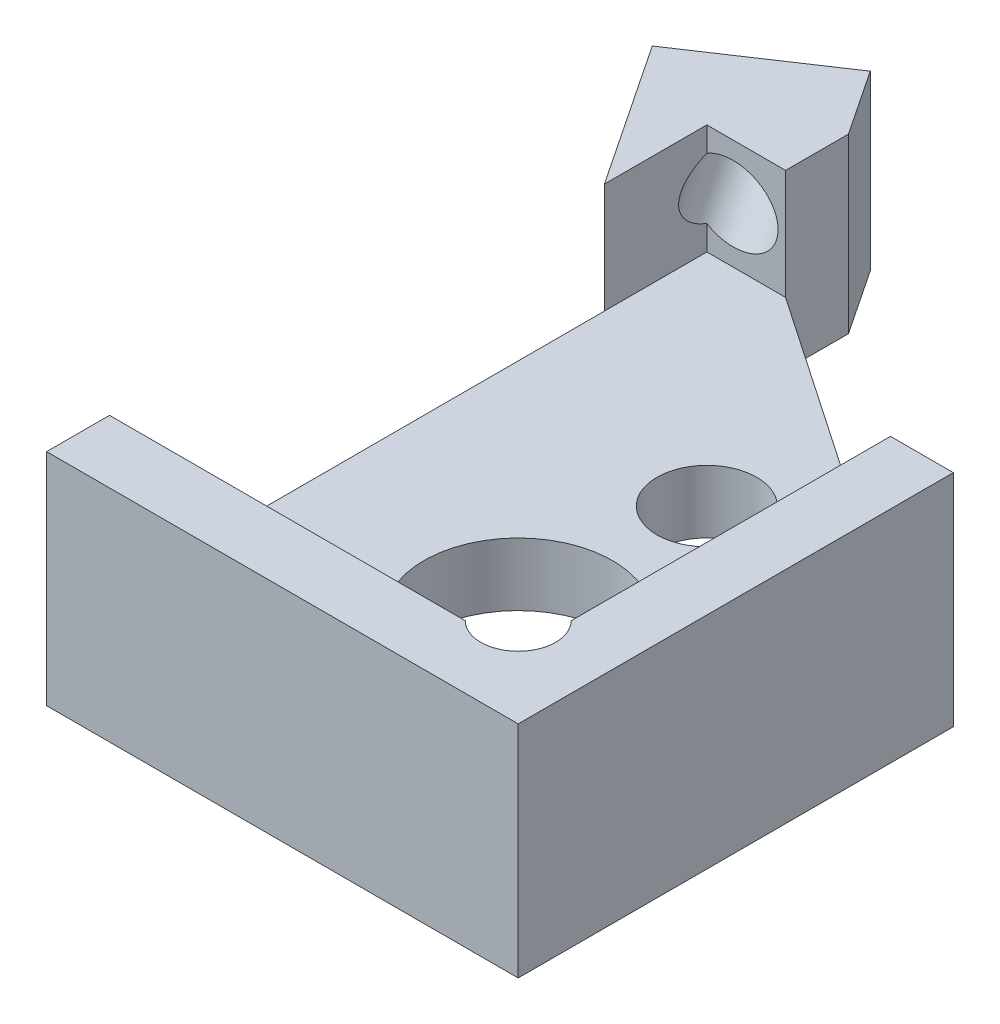
SolidWorks part; units mm, degrees
ref_plane "Front Plane" through (0, 0, 0) normal (0, 0, 1) x (1, 0, 0)
ref_plane "Top Plane" through (0, 0, 0) normal (0, 1, 0) x (1, 0, 0)
ref_plane "Right Plane" through (0, 0, 0) normal (1, 0, 0) x (0, 0, -1)
sketch "Sketch1" plane through (0, 0, 0) normal (0, 1, 0) x (1, 0, 0)
  line L7 (4.25, 5.75) -> (-4.25, 5.75)
  line L8 (4.25, 5.75) -> (4.25, -5.75)
  line L9 (4.25, -5.75) -> (-4.25, -5.75)
  line L10 (-4.25, 5.75) -> (-4.25, -5.75)
  line L11 (4.25, 5.75) -> (-4.25, -5.75) construction
  line L12 (4.25, -5.75) -> (-4.25, 5.75) construction
  point P0 (0, 0)
  point P6 (0, 0)
  dimension "D1" = 8.5
  dimension "D2" = 11.5
extrude "Boss-Extrude1" add sketch "Sketch1" along normal blind 3.5
sketch "Sketch2" plane through (0, 3.5, 0) normal (0, 1, 0) x (1, 0, 0)
  line L0 (-4.25, 5.75) -> (-4.25, -5.75) construction
  line L1 (3.25, 4.75) -> (-3.25, 4.75)
  line L2 (3.25, 4.75) -> (3.25, -4.75)
  line L3 (3.25, -4.75) -> (-3.25, -4.75)
  line L4 (-3.25, 4.75) -> (-3.25, -4.75)
  line L5 (3.25, 4.75) -> (-3.25, -4.75) construction
  line L6 (3.25, -4.75) -> (-3.25, 4.75) construction
  line L7 (4.25, 5.75) -> (-4.25, 5.75) construction
  point P0 (0, 0)
  dimension "D1" = 1
  dimension "D2" = 1
extrude "Cut-Extrude1" cut sketch "Sketch2" against normal offset from surface (2.5 mm away) 1 up to face at (0, 0, 0)
sketch "Sketch3" plane through (0, 1, 0) normal (0, 1, 0) x (1, 0, 0)
  line L0 (-3.25, -4.75) -> (3.25, -4.75) construction
  line L1 (3.25, -4.75) -> (3.25, 4.75) construction
  circle A0 centre (0.25, -1.75) radius 1.5
  dimension "D1" = 3
  dimension "D2" = 3
  dimension "D3" = 3
extrude "Cut-Extrude2" cut sketch "Sketch3" against normal through all
sketch "Sketch6" plane through (0, 3.5, 0) normal (0, 1, 0) x (1, 0, 0)
  line L0 (3.25, -4.75) -> (3.25, 4.75) construction
  line L2 (-3.25, -4.75) -> (3.25, -4.75) construction
  line L3 (3.25, -4.3291) -> (2.8291, -4.3291) construction
  line L4 (2.8291, -4.3291) -> (2.8291, -4.75) construction
  circle A3 centre (2.8291, -4.3291) radius 0.5953
  dimension "D1" = 1.1906
extrude "Cut-Extrude5" cut sketch "Sketch6" against normal up to surface (2.5 mm away) up to face at (0.25, 1, 3.25)
sketch "Sketch7" plane through (0, 1, 0) normal (0, 1, 0) x (1, 0, 0)
  line L0 (2.125, 1.25) -> (-1.625, 1.25) construction
  line L1 (-1.625, 1.25) -> (-1.625, -3.5) construction
  line L2 (-1.625, -3.5) -> (2.125, -3.5) construction
  line L3 (2.125, -3.5) -> (2.125, 1.25) construction
  line L4 (0.25, 1.25) -> (0.25, -1.75) construction
  circle A0 centre (0.25, 1.25) radius 0.7937
  circle A2 centre (-1.625, -3.5) radius 0.7938
  circle A3 centre (2.125, -3.5) radius 0.7938
  circle A4 centre (0.25, -1.75) radius 1.5 construction
  dimension "D1" = 1.5875
  dimension "D2" = 3.75
  dimension "D3" = 3
  dimension "D4" = 1.75
extrude "Cut-Extrude6" cut sketch "Sketch7" against normal through all
sketch "Sketch9" plane through (0, 3.5, 0) normal (0, 1, 0) x (1, 0, 0)
  line L0 (-2.6906, 6.7896) -> (-4.7708, 5.4028)
  line L1 (-3.4116, 4.6422) -> (-4.0015, 4.249)
  line L2 (-3.4116, 4.6422) -> (-2.5113, 5.2425)
  line L3 (-2.6906, 6.7896) -> (-1.9214, 5.6357)
  line L4 (3.25, -4.75) -> (-2.75, 4.25) construction
  line L5 (3.25, -4.75) -> (-2.75, -4.75) construction
  line L6 (-3.25, -4.75) -> (2.4081, -4.75) construction
  line L8 (-2.75, -4.75) -> (-2.75, 4.25) construction
  line L9 (-2.75, 4.25) -> (3.25, 4.25) construction
  line L10 (3.25, -3.9081) -> (3.25, 4.75) construction
  line L11 (3.25, 4.25) -> (3.25, -4.75) construction
  line L12 (-2.75, 3.6498) -> (-1.8497, 4.25) construction
  line L13 (-2.75, 3.6498) -> (-3.4116, 4.6422) construction
  line L14 (-2.2998, 3.9499) -> (-2.9615, 4.9423) construction
  line L15 (-1.9214, 5.6357) -> (-2.5113, 5.2425)
  line L16 (-4.0015, 4.249) -> (-4.7708, 5.4028)
  line L17 (-2.9615, 4.9423) -> (-3.7307, 6.0962) construction
  arc A0 (2.4081, -4.75) -> (3.25, -3.9081) centre (2.8291, -4.3291) ccw construction
  dimension "D1" = 6
  dimension "D2" = 9
  dimension "D3" = 1.082
  dimension "D4" = 2.5
extrude "Boss-Extrude2" add sketch "Sketch9" against normal up to surface (3.5 mm away) up to face at (2.125, 0, 4.2938)
sketch "Sketch14" plane through (0, 3.5, 0) normal (0, 1, 0) x (1, 0, 0)
  line L1 (-6.2326, 2.1835) -> (-0.2674, 2.1835)
  line L2 (-6.2326, 2.1835) -> (-6.2326, 7.3165)
  line L3 (-6.2326, 7.3165) -> (-0.2674, 7.3165)
  line L4 (-0.2674, 2.1835) -> (-0.2674, 7.3165)
  line L5 (-6.2326, 2.1835) -> (-0.2674, 7.3165) construction
  line L6 (-6.2326, 7.3165) -> (-0.2674, 2.1835) construction
  point P0 (-3.25, 4.75)
extrude "Cut-Extrude8" cut sketch "Sketch14" against normal blind 0.75
sketch "Sketch10" plane through (-3.9615, 0, -5.9423) normal (-0.5547, 0, -0.8321) x (-0.8321, 0, 0.5547)
  line L0 (-0.2774, 1) -> (-0.2774, 1.875) construction
  line L1 (-1.5274, 2.75) -> (0.9726, 2.75) construction
  line L2 (-0.2774, 1.875) -> (-0.2774, 2.75) construction
  line L4 (-0.2774, 1) -> (-0.2774, 0) construction
  line L5 (-1.5274, 0) -> (0.9726, 0) construction
  dimension "D1" = 1
hole_wizard "Tap Drill for #0-80 Tap1" positions "Sketch12" profile "Sketch11" hole size "#0-80" standard "ANSI Inch"
sketch "Sketch12" plane through (-3.9615, 0, -5.9423) normal (-0.5547, 0, -0.8321) x (-0.8321, 0, 0.5547)
  point P0 (-0.2774, 1.875)
sketch "Sketch11" plane through (-3.7307, 1.875, -6.0962) normal (0, 1, 0) x (-0.8321, 0, 0.5547)
  line L0 (0, 0) -> (0, 7.4679)
  line L1 (0, 7.4679) -> (0.5956, 7.11)
  line L2 (0.5956, 7.11) -> (0.5956, 0)
  line L5 (0.5956, 0) -> (0, 0)
  line L10 (0, 7.4679) -> (-0.5956, 7.11) construction
  line L11 (0, -6.35) -> (0, 107.95) construction
  dimension "Hole Dia." = 1.1913
  dimension "Hole Depth" = 7.11
  dimension "Drill Angle" = 118
sketch "Sketch13" plane through (0, 3.5, 0) normal (0, 1, 0) x (1, 0, 0)
  line L0 (-1.9976, 5.75) -> (-1.9976, 4.75)
  line L2 (-1.625, -3.5) -> (-3.25, -3.5) construction
  line L3 (3.25, 1.1708) -> (4.25, 1.1708)
  line L4 (4.25, -5.75) -> (4.25, 5.75) construction
  line L5 (4.25, 1.1708) -> (4.25, 5.75)
  line L6 (4.25, 5.75) -> (-1.9976, 5.75)
  line L7 (-4.25, 4.6217) -> (-3.25, 3.1217)
  line L8 (-3.25, 2.1835) -> (-3.25, -4.75) construction
  line L9 (-4.25, 2.1835) -> (-4.25, -5.75) construction
  line L10 (-3.25, 3.1217) -> (-3.25, -5.75)
  line L11 (-4.25, -5.75) -> (4.25, -5.75) construction
  line L12 (-3.25, -5.75) -> (-4.25, -5.75)
  line L13 (-4.25, -5.75) -> (-4.25, 4.6217)
  line L15 (-4.7708, 5.4028) -> (-4.25, 4.6217) construction
  line L17 (-1.9976, 4.75) -> (3.25, 1.1708)
  line L18 (3.25, -3.9081) -> (3.25, 4.75) construction
  line L20 (0.25, 1.25) -> (1.1656, 2.5925) construction
  line L23 (3.25, 4.75) -> (-0.2674, 4.75) construction
  point P2 (0, 0)
extrude "Cut-Extrude7" cut sketch "Sketch13" against normal up to next
